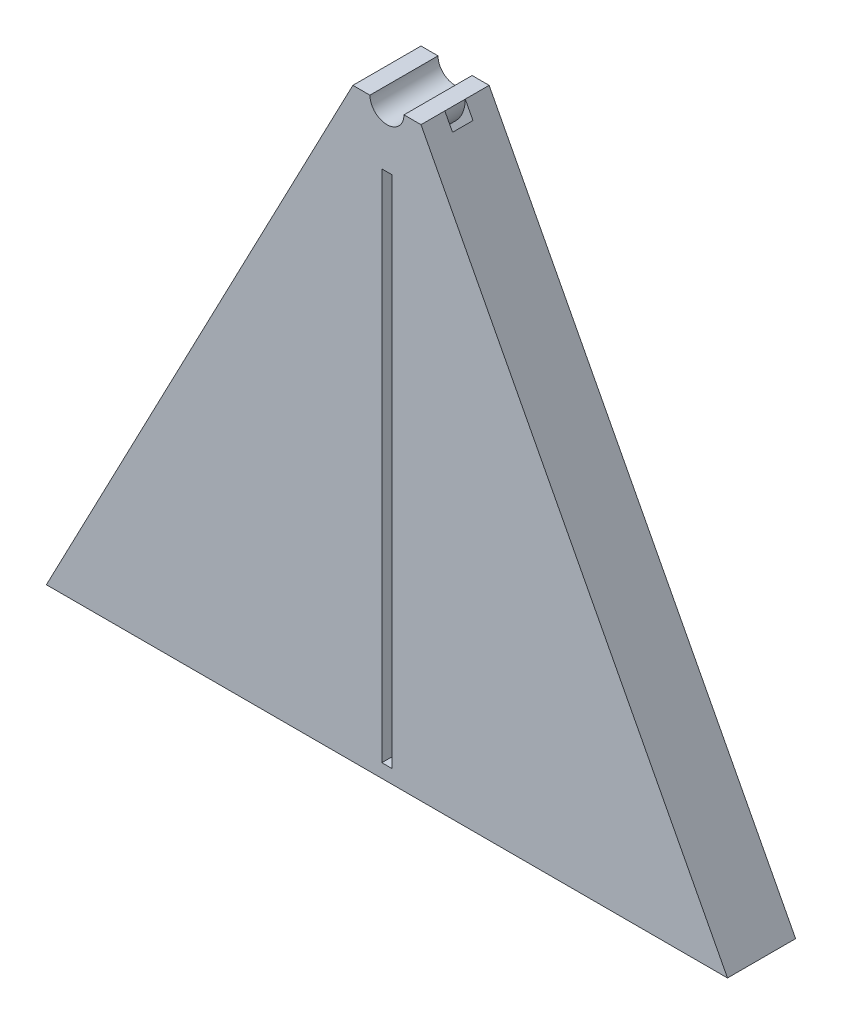
SolidWorks part; units mm, degrees
ref_plane "Front Plane" through (0, 0, 0) normal (0, 0, 1) x (1, 0, 0)
ref_plane "Top Plane" through (0, 0, 0) normal (0, 1, 0) x (1, 0, 0)
ref_plane "Right Plane" through (0, 0, 0) normal (1, 0, 0) x (0, 0, -1)
sketch "Sketch1" plane through (0, 0, 0) normal (0, 0, 1) x (1, 0, 0)
  line L0 (-50, -86) -> (50, -86)
  line L1 (50, -86) -> (5, 0)
  line L2 (5, 0) -> (2.5, 0)
  line L3 (-5, 0) -> (-50, -86)
  line L4 (0, -86) -> (0, 0) construction
  line L5 (-2.5, 0) -> (-5, 0)
  arc A0 (-2.5, 0) -> (2.5, 0) centre (0, 0) ccw
  point P10 (0, 0)
  dimension "D1" = 5
  dimension "D2" = 86
  dimension "D3" = 100
  dimension "D4" = 5
  dimension "D5" = 5
extrude "Boss-Extrude1" add sketch "Sketch1" along normal blind 10
sketch "Sketch2" plane through (0, 0, 10) normal (0, 0, 1) x (1, 0, 0)
  circle A0 centre (0, 0) radius 5
  circle A1 centre (0, 0) radius 6.5
  arc A2 (-2.5, 0) -> (2.5, 0) centre (0, 0) ccw construction
  dimension "D1" = 2.5
  dimension "D2" = 1.5
extrude "Cut-Extrude1" cut sketch "Sketch2" against normal blind 6.5
sketch "Sketch3" plane through (0, 0, 10) normal (0, 0, 1) x (1, 0, 0)
  line L0 (5, 0) -> (6.1305, -2.1604)
  line L1 (-5, 0) -> (-6.1305, -2.1604)
  line L5 (-6.1305, -2.1604) -> (-50, -86)
  line L6 (-50, -86) -> (50, -86)
  line L7 (50, -86) -> (6.1305, -2.1604)
  arc A0 (-5, 0) -> (5, 0) centre (0, 0) ccw construction
  arc A1 (-5, 0) -> (5, 0) centre (0, 0) ccw
  arc A3 (-6.1305, -2.1604) -> (6.1305, -2.1604) centre (0, 0) ccw
  arc A4 (-6.1305, -2.1604) -> (6.1305, -2.1604) centre (0, 0) ccw
  dimension "D1" = 0
extrude "Boss-Extrude2" add sketch "Sketch3" against normal blind 3.5
sketch "Sketch4" plane through (0, 0, 10) normal (0, 0, 1) x (1, 0, 0)
  line L0 (0, -8.5) -> (0, 0) construction
  line L1 (-0.75, -8.5) -> (0.75, -8.5)
  line L2 (-5, 0) -> (-6.1305, -2.1604)
  line L3 (6.1305, -2.1604) -> (5, 0)
  line L4 (-5, 0) -> (-6.1305, -2.1604) construction
  line L5 (6.1305, -2.1604) -> (5, 0) construction
  line L6 (-0.75, -8.5) -> (-0.75, -84)
  line L7 (-0.75, -84) -> (0.75, -84)
  line L8 (0.75, -8.5) -> (0.75, -84)
  line L9 (-50, -86) -> (50, -86) construction
  arc A2 (-6.1305, -2.1604) -> (6.1305, -2.1604) centre (0, 0) ccw
  arc A3 (-5, 0) -> (5, 0) centre (0, 0) ccw
  arc A4 (-6.1305, -2.1604) -> (6.1305, -2.1604) centre (0, 0) ccw construction
  arc A5 (-5, 0) -> (5, 0) centre (0, 0) ccw construction
  point P15 (0, 0)
  dimension "D2" = 8.5
  dimension "D3" = 2
  dimension "D4" = 1.5
  dimension "D1" = 0
extrude "Cut-Extrude2" cut sketch "Sketch4" against normal through all
